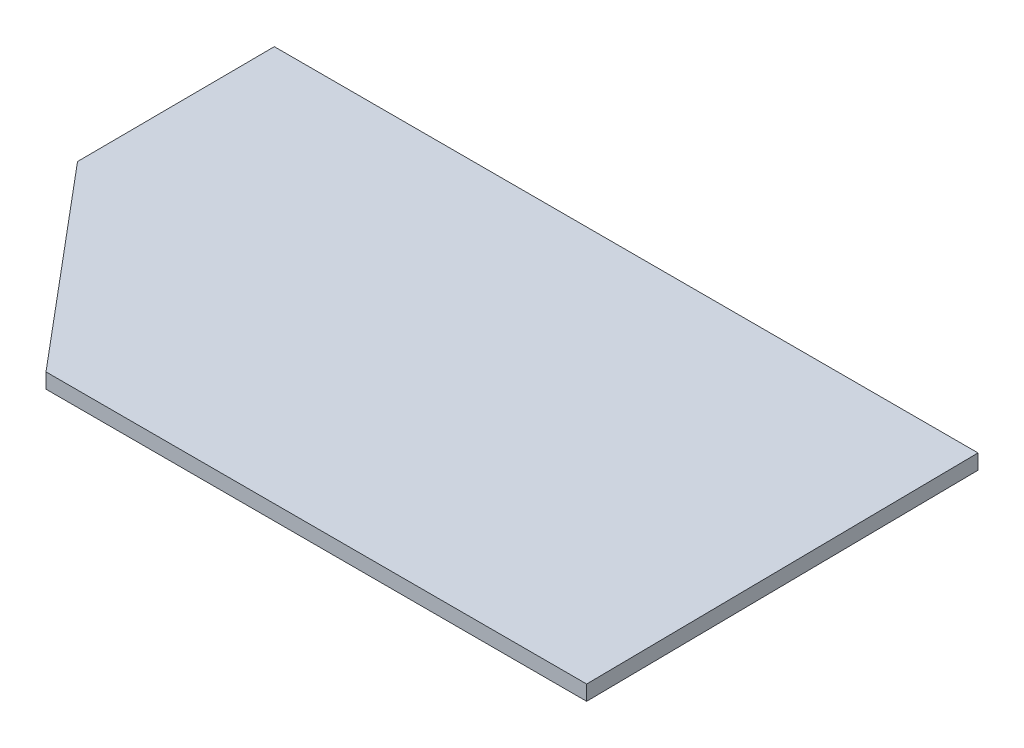
SolidWorks part; units mm, degrees
ref_plane "Plan de face" through (0, 0, 0) normal (0, 0, 1) x (1, 0, 0)
ref_plane "Plan de dessus" through (0, 0, 0) normal (0, 1, 0) x (1, 0, 0)
ref_plane "Plan de droite" through (0, 0, 0) normal (1, 0, 0) x (0, 0, -1)
sketch "Esquisse1" plane through (0, 0, 0) normal (0, 1, 0) x (1, 0, 0)
  line L0 (-22.1631, 26.3618) -> (0, 0)
  line L1 (0, 0) -> (72.018, 0)
  line L2 (71.4216, 52.7235) -> (-22.3082, 52.7235)
  line L3 (-22.3082, 52.7235) -> (-22.1631, 26.3618)
  line L4 (72.018, 0) -> (71.4216, 52.7235)
  point P5 (0, 0)
extrude "Boss.-Extru.1" add sketch "Esquisse1" along normal blind 2
